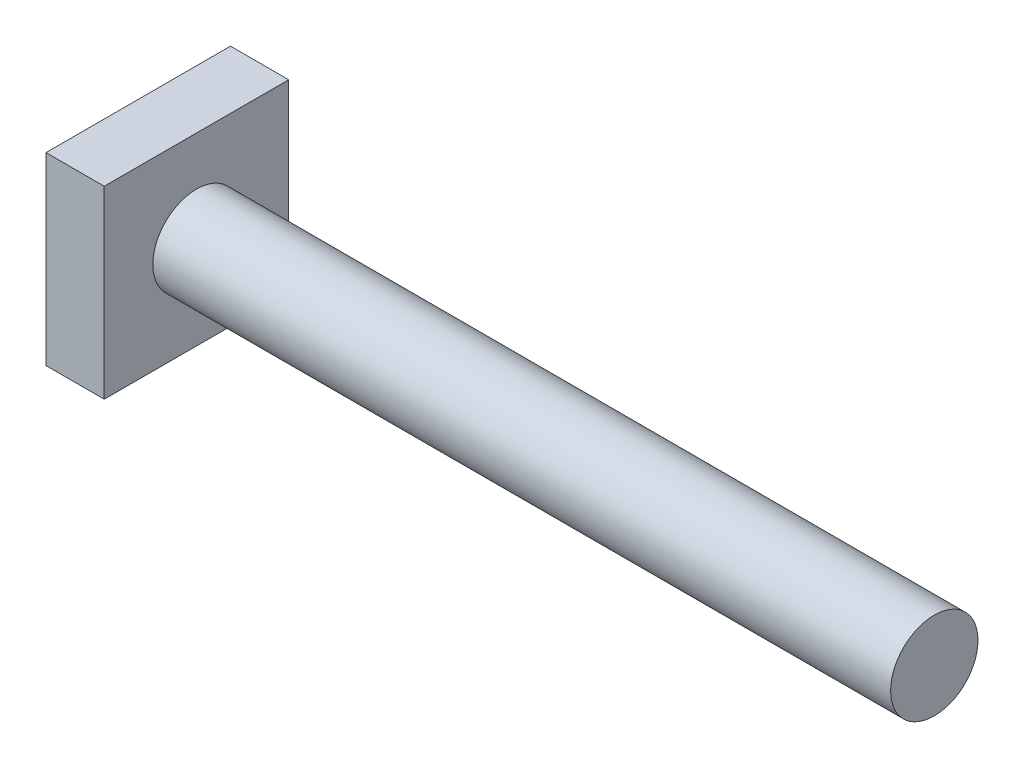
SolidWorks part; units mm, degrees
ref_plane "Front Plane" through (0, 0, 0) normal (0, 0, 1) x (1, 0, 0)
ref_plane "Top Plane" through (0, 0, 0) normal (0, 1, 0) x (1, 0, 0)
ref_plane "Right Plane" through (0, 0, 0) normal (1, 0, 0) x (0, 0, -1)
sketch "Sketch1" plane through (0, 0, 0) normal (1, 0, 0) x (0, 0, -1)
  line L1 (-9.5, -9.5) -> (9.5, -9.5)
  line L2 (-9.5, -9.5) -> (-9.5, 9.5)
  line L3 (-9.5, 9.5) -> (9.5, 9.5)
  line L4 (9.5, -9.5) -> (9.5, 9.5)
  line L5 (-9.5, -9.5) -> (9.5, 9.5) construction
  line L6 (-9.5, 9.5) -> (9.5, -9.5) construction
  point P0 (0, 0)
  dimension "D1" = 19
extrude "Boss-Extrude1" add sketch "Sketch1" along normal blind 6
sketch "Sketch2" plane through (6, 0, 0) normal (1, 0, 0) x (0, 0, -1)
  circle A0 centre (0, 0) radius 4.5
  dimension "D1" = 9
extrude "Boss-Extrude2" add sketch "Sketch2" along normal blind 76
